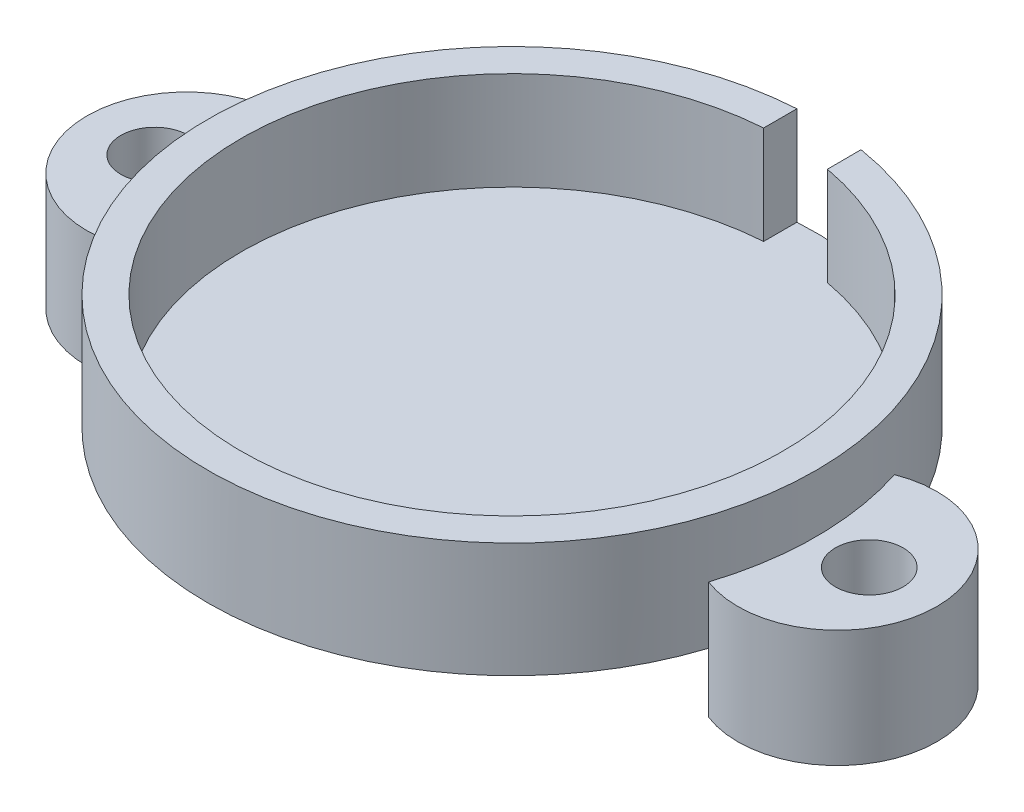
SolidWorks part; units mm, degrees
ref_plane "Front Plane" through (0, 0, 0) normal (0, 0, 1) x (1, 0, 0)
ref_plane "Top Plane" through (0, 0, 0) normal (0, 1, 0) x (1, 0, 0)
ref_plane "Right Plane" through (0, 0, 0) normal (1, 0, 0) x (0, 0, -1)
sketch "Sketch1" plane through (0, 0, 0) normal (0, 1, 0) x (1, 0, 0)
  circle A0 centre (0, 0) radius 58.166
  dimension "D1" = 116.332
extrude "Boss-Extrude1" add sketch "Sketch1" along normal blind 21.971 contours A0
sketch "Sketch3" plane through (0, 21.971, 0) normal (0, 1, 0) x (1, 0, 0)
  circle A0 centre (0, 0) radius 51.816
  dimension "D1" = 103.632
extrude "Cut-Extrude2" cut sketch "Sketch3" against normal blind 18.796
sketch "Sketch6" plane through (0, 21.971, 0) normal (0, 1, 0) x (1, 0, 0)
  line L0 (9.363, 50.963) -> (9.3408, 57.4111)
  line L1 (-3.5704, 51.6928) -> (-3.5704, 58.0563)
  arc A0 (9.3408, 57.4111) -> (-3.5704, 58.0563) centre (0, 0) ccw
  circle A1 centre (0, 0) radius 58.166 construction
  circle A2 centre (0, 0) radius 58.166 construction
  arc A3 (9.363, 50.963) -> (-3.5704, 51.6928) centre (0, 0) ccw
  circle A4 centre (0, 0) radius 51.816 construction
  circle A5 centre (0, 0) radius 51.816 construction
  point P12 (0, 51.689)
  point P15 (0, 53.2765)
  point P16 (-3.5704, 51.6928)
  point P17 (-3.5704, 58.0563)
  dimension "D1" = 12.954
  dimension "D2" = 12.954
extrude "Cut-Extrude7" cut sketch "Sketch6" against normal blind 18.796
sketch "Sketch7" plane through (0, 0, 0) normal (0, -1, 0) x (1, 0, 0)
  circle A5 centre (0, 0) radius 58.166 construction
  arc A7 (55.3829, -17.7769) -> (55.3829, 17.7769) centre (62.23, 0) ccw
  arc A8 (-55.3829, 17.7769) -> (-55.3829, -17.7769) centre (-62.23, 0) ccw
  circle A11 centre (-68.3238, 0) radius 6.477
  arc A12 (-55.3829, -17.7769) -> (-55.3829, 17.7769) centre (0, 0) cw
  arc A13 (55.3829, 17.7769) -> (55.3829, -17.7769) centre (0, 0) cw
  circle A14 centre (68.326, 0) radius 6.477
  dimension "D2" = 62.23
  dimension "D3" = 62.23
  dimension "D4" = 38.1
  dimension "D5" = 12.954
  dimension "D6" = 12.954
  dimension "D7" = 68.3238
  dimension "D1" = 38.1
  dimension "D8" = 68.326
extrude "Boss-Extrude3" add sketch "Sketch7" against normal blind 10.9855 and the other way blind 11.43
